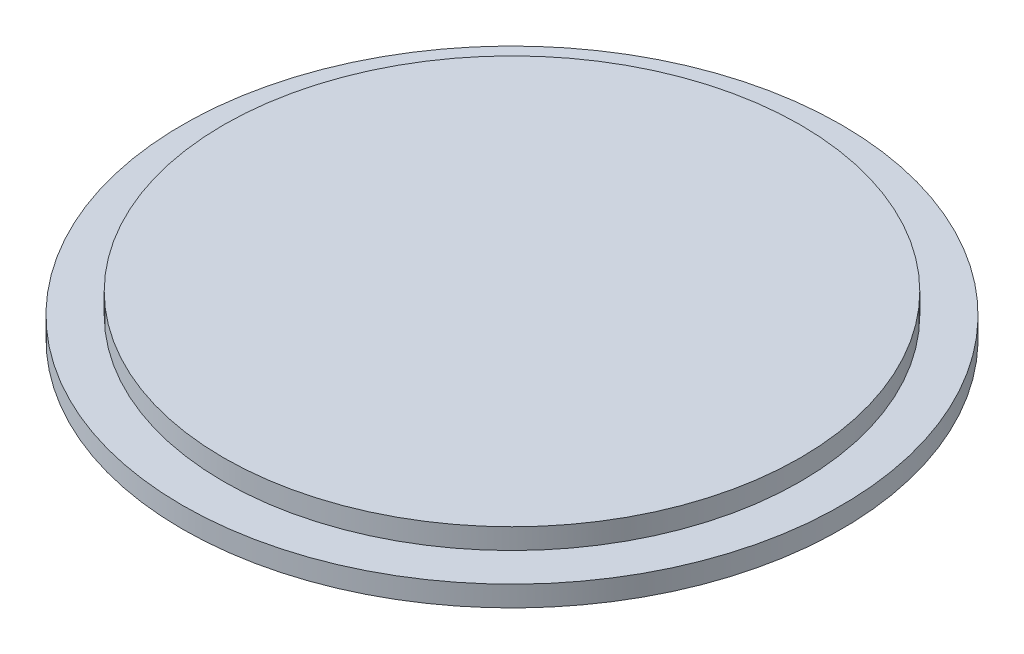
SolidWorks part; units mm, degrees
ref_plane "Спереди" through (0, 0, 0) normal (0, 0, 1) x (1, 0, 0)
ref_plane "Сверху" through (0, 0, 0) normal (0, 1, 0) x (1, 0, 0)
ref_plane "Справа" through (0, 0, 0) normal (1, 0, 0) x (0, 0, -1)
sketch "Эскиз1" plane through (0, 0, 0) normal (0, 0, 1) x (1, 0, 0)
  line L0 (0, 0) -> (0, 2)
  line L1 (0, 2) -> (14, 2)
  line L2 (14, 2) -> (14, 1)
  line L3 (14, 1) -> (16, 1)
  line L4 (16, 1) -> (16, 0)
  line L5 (16, 0) -> (0, 0)
  dimension "D1" = 16
  dimension "D2" = 14
  dimension "D3" = 2
  dimension "D4" = 1
revolve "Повернуть1" add sketch "Эскиз1" angle 360 about L0
